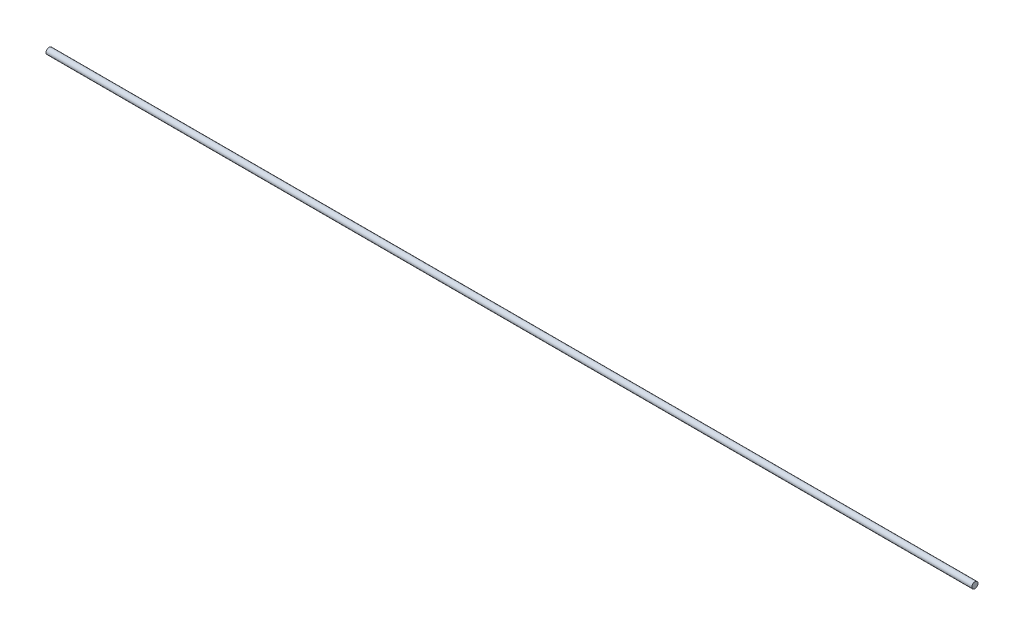
SolidWorks part; units mm, degrees
ref_plane "Front Plane" through (0, 0, 0) normal (0, 0, 1) x (1, 0, 0)
ref_plane "Top Plane" through (0, 0, 0) normal (0, 1, 0) x (1, 0, 0)
ref_plane "Right Plane" through (0, 0, 0) normal (1, 0, 0) x (0, 0, -1)
sketch "Sketch1" plane through (0, 0, 0) normal (1, 0, 0) x (0, 0, -1)
  circle A0 centre (0, 0) radius 0.06
  dimension "D1" = 0.12
extrude "Boss-Extrude1" add sketch "Sketch1" along normal blind 18 contours A0
